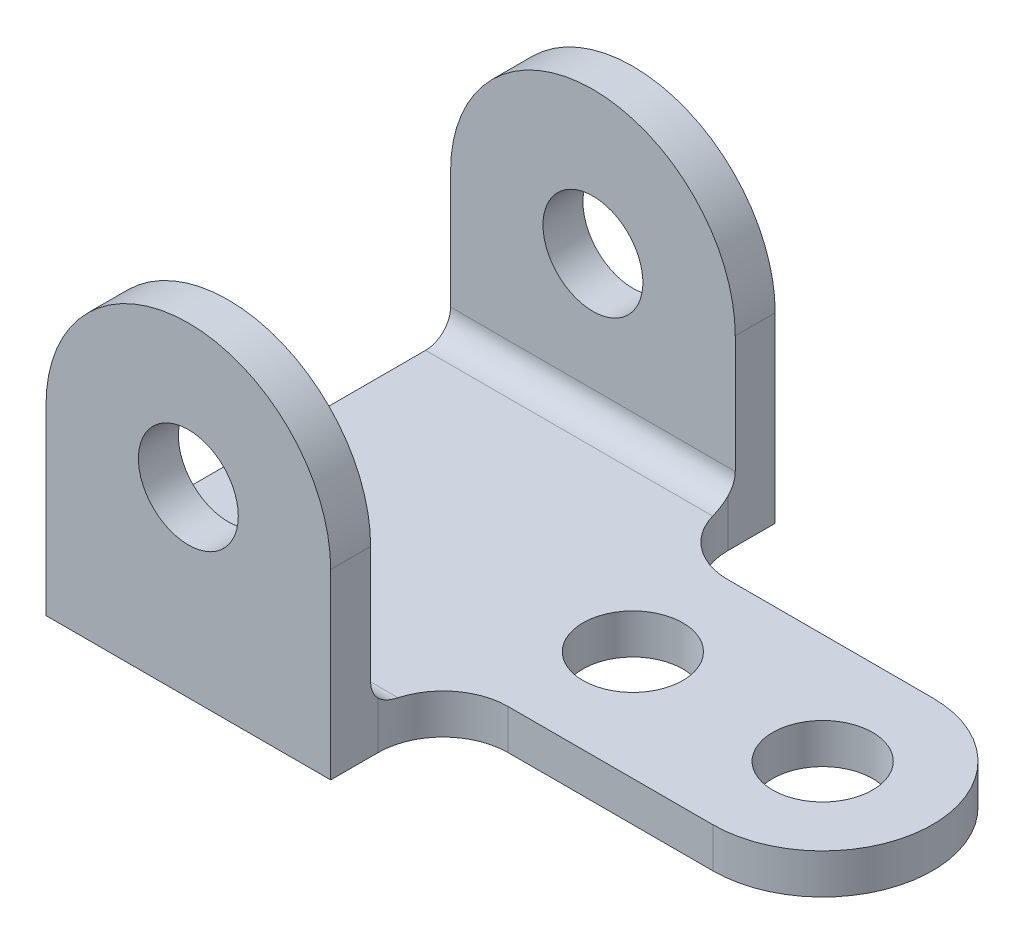
SolidWorks part; units mm, degrees
material "Plain Carbon Steel"
ref_plane "Front Plane" through (0, 0, 0) normal (0, 0, 1) x (1, 0, 0)
ref_plane "Top Plane" through (0, 0, 0) normal (0, 1, 0) x (1, 0, 0)
ref_plane "Right Plane" through (0, 0, 0) normal (1, 0, 0) x (0, 0, -1)
sketch "Sketch2" plane through (0, 0, 0) normal (0, 1, 0) x (1, 0, 0)
  line L0 (0, 0) -> (0, 89)
  line L1 (0, 0) -> (57, 0)
  line L2 (57, 0) -> (57, 9.5)
  line L3 (70, 22.5) -> (111, 22.5)
  line L5 (111, 66.5) -> (70, 66.5)
  line L6 (57, 79.5) -> (57, 89)
  line L7 (57, 89) -> (0, 89)
  arc A0 (57, 9.5) -> (70, 22.5) centre (70, 9.5) cw
  arc A1 (70, 66.5) -> (57, 79.5) centre (70, 79.5) cw
  circle A2 centre (73, 44.5) radius 10
  circle A3 centre (111, 44.5) radius 10
  arc A4 (111, 66.5) -> (111, 22.5) centre (111, 44.5) cw
  point P21 (0, 44.5)
  dimension "D2" = 13
  dimension "D3" = 20
  dimension "D4" = 22
  dimension "D1" = 89
  dimension "D5" = 38
  dimension "D6" = 16
  dimension "D7" = 57
extrude "Boss-Extrude1" add sketch "Sketch2" along normal blind 8
sketch "Sketch3" plane through (0, 0, 0) normal (0, 0, 1) x (1, 0, 0)
  line L1 (0, 0) -> (57, 0)
  line L2 (0, 0) -> (0, 36.5)
  line L4 (57, 0) -> (57, 36.5)
  arc A0 (0, 36.5) -> (57, 36.5) centre (28.5, 36.5) cw
  circle A1 centre (28.5, 36.5) radius 10
  dimension "D2" = 36.5
  dimension "D1" = 28.5
  dimension "D3" = 20
extrude "Boss-Extrude2" add sketch "Sketch3" against normal blind 8
sketch "Sketch4" plane through (0, 0, -89) normal (0, 0, -1) x (-1, 0, 0)
  line L3 (-57, 8) -> (0, 8)
  line L4 (0, 8) -> (0, 36.5)
  line L5 (-57, 36.5) -> (-57, 8)
  line L6 (-57, 8) -> (0, 8)
  line L7 (0, 8) -> (0, 36.5)
  line L8 (-57, 36.5) -> (-57, 8)
  circle A0 centre (-28.5, 36.5) radius 10 construction
  arc A1 (0, 36.5) -> (-57, 36.5) centre (-28.5, 36.5) ccw
  arc A2 (0, 36.5) -> (-57, 36.5) centre (-28.5, 36.5) ccw
  circle A3 centre (-28.5, 36.5) radius 10
  dimension "D1" = 0
extrude "Boss-Extrude3" add sketch "Sketch4" against normal blind 8
fillet "Fillet1" radius 5 2 edges at (28.5, 8, -8) (28.5, 8, -81)
